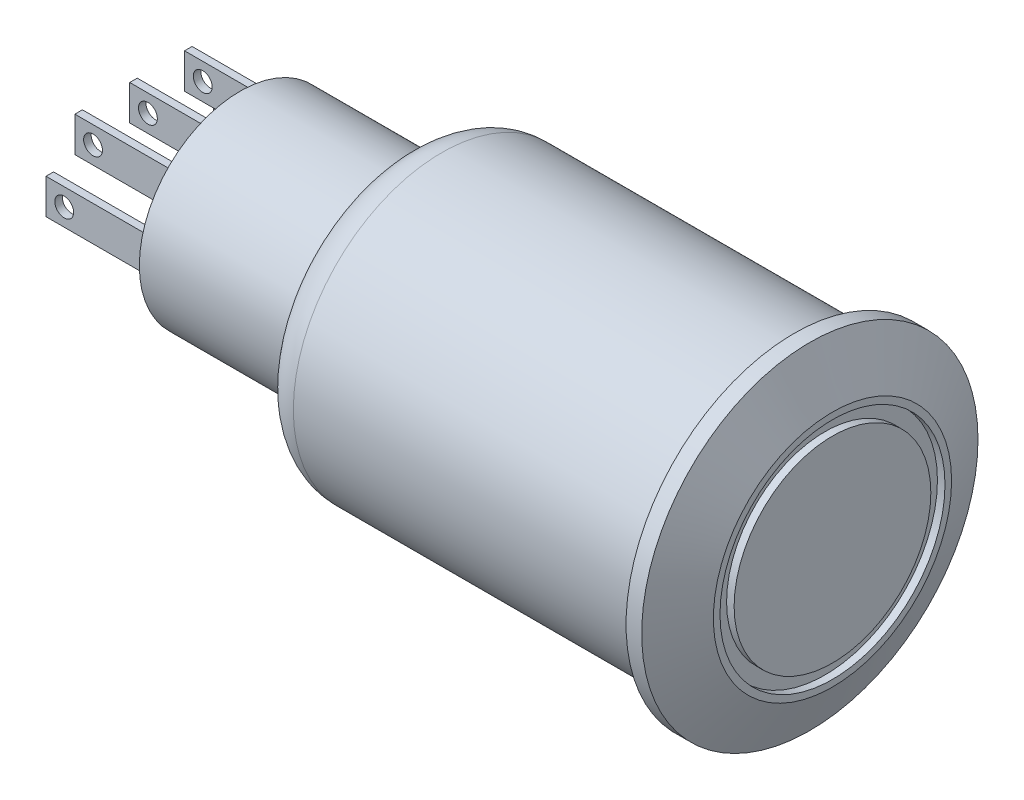
SolidWorks part; units mm, degrees
ref_plane "Front Plane" through (0, 0, 0) normal (0, 0, 1) x (1, 0, 0)
ref_plane "Top Plane" through (0, 0, 0) normal (0, 1, 0) x (1, 0, 0)
ref_plane "Right Plane" through (0, 0, 0) normal (1, 0, 0) x (0, 0, -1)
sketch "Sketch1" plane through (0, 0, 0) normal (1, 0, 0) x (0, 0, -1)
  circle A0 centre (0, 0) radius 7.875
  dimension "D1" = 15.75
extrude "Boss-Extrude1" add sketch "Sketch1" along normal blind 20.68
sketch "Sketch2" plane through (20.68, 0, 0) normal (1, 0, 0) x (0, 0, -1)
  circle A0 centre (0, 0) radius 8.915
  dimension "D1" = 17.83
extrude "Boss-Extrude2" add sketch "Sketch2" along normal blind 2.03
sketch "Sketch3" plane through (22.71, 0, 0) normal (1, 0, 0) x (0, 0, -1)
  circle A0 centre (0, 0) radius 5.215
  circle A2 centre (0, 0) radius 5.965
  dimension "D1" = 10.43
  dimension "D2" = 11.93
extrude "Cut-Extrude1" cut sketch "Sketch3" against normal blind 0.4
chamfer "Chamfer1" distance 1.2 distance2 2.6 1 edges at (22.71, 0, -8.915)
sketch "Sketch4" plane through (0, 0, 0) normal (-1, 0, 0) x (0, 0, 1)
  circle A0 centre (0, 0) radius 5.34
  dimension "D1" = 10.68
extrude "Boss-Extrude3" add sketch "Sketch4" along normal blind 8.7
sketch "Sketch5" plane through (-8.7, 0, 0) normal (-1, 0, 0) x (0, 0, 1)
  line L0 (-0.0992, 2.086) -> (49999.9008, 2.086) construction
  line L2 (-3.1082, 3.016) -> (-2.7082, 3.016)
  line L3 (-3.1082, 3.016) -> (-3.1082, 1.156)
  line L4 (-3.1082, 1.156) -> (-2.7082, 1.156)
  line L5 (-2.7082, 3.016) -> (-2.7082, 1.156)
  line L6 (-3.1082, 3.016) -> (-2.7082, 1.156) construction
  line L7 (-3.1082, 1.156) -> (-2.7082, 3.016) construction
  line L11 (0, 0) -> (0, 50000) construction
  line L12 (0.2, 1.156) -> (-0.2, 1.156)
  line L13 (0.2, 1.156) -> (0.2, 3.016)
  line L14 (0.2, 3.016) -> (-0.2, 3.016)
  line L15 (-0.2, 1.156) -> (-0.2, 3.016)
  line L16 (0.2, 1.156) -> (-0.2, 3.016) construction
  line L17 (0.2, 3.016) -> (-0.2, 1.156) construction
  line L18 (3.1082, 1.156) -> (2.7082, 1.156)
  line L19 (2.7082, 3.016) -> (2.7082, 1.156)
  line L20 (3.1082, 3.016) -> (2.7082, 3.016)
  line L21 (3.1082, 3.016) -> (3.1082, 1.156)
  line L22 (0, 0) -> (-50000, 0) construction
  line L23 (4.6379, -0.93) -> (4.2379, -0.93)
  line L24 (-4.6379, 0.93) -> (-4.2379, 0.93)
  line L25 (-4.6379, 0.93) -> (-4.6379, -0.93)
  line L26 (-4.6379, -0.93) -> (-4.2379, -0.93)
  line L27 (-4.2379, 0.93) -> (-4.2379, -0.93)
  line L28 (-4.6379, 0.93) -> (-4.2379, -0.93) construction
  line L29 (-4.6379, -0.93) -> (-4.2379, 0.93) construction
  line L30 (4.2379, 0.93) -> (4.2379, -0.93)
  line L31 (4.6379, 0.93) -> (4.2379, 0.93)
  line L32 (4.6379, 0.93) -> (4.6379, -0.93)
  point P2 (-2.9082, 2.086)
  point P7 (0, 2.086)
  point P21 (-4.4379, 0)
  dimension "D1" = 0.4
  dimension "D2" = 1.86
  dimension "D3" = 0.4
  dimension "D4" = 0.4
  dimension "D5" = 1.86
extrude "Boss-Extrude4" add sketch "Sketch5" along normal blind 5.65
sketch "Sketch6" plane through (0, 0, -4.6379) normal (0, 0, -1) x (-1, 0, 0)
  circle A0 centre (13.385, 0) radius 0.5
  circle A1 centre (13.385, 2.086) radius 0.5
extrude "Cut-Extrude2" cut sketch "Sketch6" against normal through all
fillet "Fillet1" radius 2 1 edges at (0, 0, -7.875)
